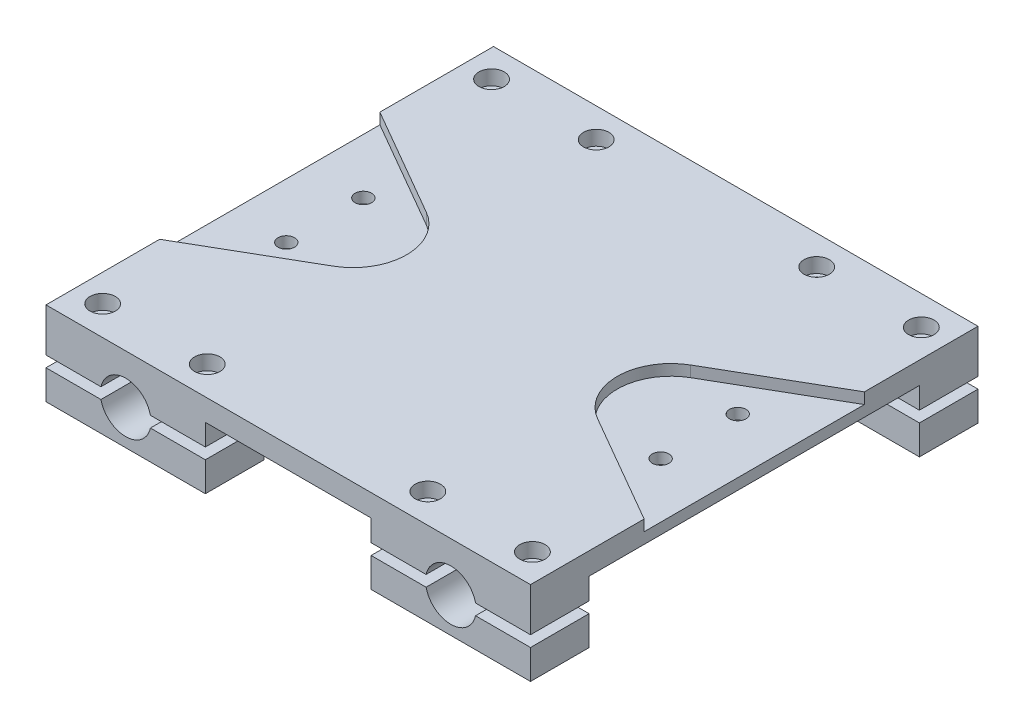
SolidWorks part; units mm, degrees
ref_plane "Front Plane" through (0, 0, 0) normal (0, 0, 1) x (1, 0, 0)
ref_plane "Top Plane" through (0, 0, 0) normal (0, 1, 0) x (1, 0, 0)
ref_plane "Right Plane" through (0, 0, 0) normal (1, 0, 0) x (0, 0, -1)
sketch "Sketch1" plane through (0, 0, 0) normal (0, 0, 1) x (1, 0, 0)
  line L0 (73.8188, 0) -> (0, 0) construction
  line L1 (-110, -15.875) -> (110, -15.875)
  line L2 (-110, -15.875) -> (-110, 15.875)
  line L3 (-110, 15.875) -> (110, 15.875)
  line L4 (110, -15.875) -> (110, 15.875)
  line L5 (-110, -15.875) -> (110, 15.875) construction
  line L6 (-110, 15.875) -> (110, -15.875) construction
  line L7 (0, 0) -> (-73.8187, 0) construction
  circle A1 centre (-73.8187, 0) radius 11.5
  circle A2 centre (73.8188, 0) radius 11.5
  point P0 (0, 0)
  dimension "D1" = 147.6375
  dimension "D4" = 23
  dimension "D2" = 31.75
  dimension "D3" = 220
extrude "Boss-Extrude1" add sketch "Sketch1" along normal blind 203.2
sketch "Sketch3" plane through (0, 0, 203.2) normal (0, 0, 1) x (1, 0, 0)
  line L0 (110, -15.875) -> (110, 15.875) construction
  line L1 (-110, 15.875) -> (110, 15.875)
  line L2 (-110, 15.875) -> (-110, 22.225)
  line L3 (-110, 22.225) -> (110, 22.225)
  line L4 (110, 15.875) -> (110, 22.225)
  dimension "D1" = 6.35
extrude "Boss-Extrude2" add sketch "Sketch3" against normal up to surface (203.2 mm away) up to face at (-62.3188, 0, 0)
sketch "Sketch4" plane through (-110, 0, 0) normal (-1, 0, 0) x (0, 0, 1)
  line L0 (203.2, -15.875) -> (0, -15.875) construction
  line L1 (26.6, -15.875) -> (176.6, -15.875)
  line L2 (26.6, -15.875) -> (26.6, 12.225)
  line L3 (26.6, 12.225) -> (176.6, 12.225)
  line L4 (176.6, -15.875) -> (176.6, 12.225)
  line L5 (0, 0) -> (26.6, 0) construction
  line L6 (26.6, 0) -> (176.6, 0) construction
  line L7 (176.6, 0) -> (203.2, 0) construction
  line L8 (203.2, 22.225) -> (203.2, -15.875) construction
  line L9 (0, 22.225) -> (203.2, 22.225) construction
  dimension "D1" = 10
  dimension "D2" = 150
extrude "Cut-Extrude1" cut sketch "Sketch4" against normal blind 253.2
sketch "Sketch5" plane through (0, 0, 0) normal (0, 0, -1) x (-1, 0, 0)
  line L0 (110, -15.875) -> (-110, -15.875) construction
  line L1 (-37.6375, -15.875) -> (37.6375, -15.875)
  line L2 (-37.6375, -15.875) -> (-37.6375, 12.225)
  line L3 (-37.6375, 12.225) -> (37.6375, 12.225)
  line L4 (37.6375, -15.875) -> (37.6375, 12.225)
  line L5 (-110, 22.225) -> (110, 22.225) construction
  line L6 (0, 0) -> (-37.6375, 0) construction
  line L7 (0, 0) -> (37.6375, 0) construction
  line L8 (-37.6375, 0) -> (-73.8188, 0) construction
  line L9 (-73.8188, 0) -> (-110, 0) construction
  line L10 (-110, -15.875) -> (-110, 22.225) construction
  dimension "D1" = 10
extrude "Cut-Extrude2" cut sketch "Sketch5" against normal blind 203.2
sketch "Sketch6" plane through (0, -15.875, 0) normal (0, -1, 0) x (1, 0, 0)
  line L0 (-110, 189.9) -> (-97.5688, 189.9) construction
  line L2 (-97.5688, 189.9) -> (-50.0688, 189.9) construction
  line L3 (-50.0688, 189.9) -> (-37.6375, 189.9) construction
  line L5 (-110, 13.3) -> (-97.5688, 13.3) construction
  line L6 (-110, 26.6) -> (-110, 0) construction
  line L7 (-97.5688, 13.3) -> (-50.0688, 13.3) construction
  line L8 (-50.0688, 13.3) -> (-37.6375, 13.3) construction
  line L9 (-37.6375, 26.6) -> (-37.6375, 0) construction
  line L10 (37.6375, 203.2) -> (37.6375, 176.6) construction
  line L11 (37.6375, 26.6) -> (37.6375, 0) construction
  line L12 (37.6375, 13.3) -> (50.0688, 13.3) construction
  line L13 (50.0688, 13.3) -> (97.5687, 13.3) construction
  line L14 (97.5687, 13.3) -> (110, 13.3) construction
  line L16 (-62.3188, 203.2) -> (-85.3187, 203.2) construction
  line L18 (110, 189.9) -> (97.5687, 189.9) construction
  line L19 (97.5687, 189.9) -> (50.0688, 189.9) construction
  line L20 (50.0688, 189.9) -> (37.6375, 189.9) construction
  line L22 (-62.3188, 203.2) -> (-85.3187, 203.2)
  line L23 (-85.3187, 203.2) -> (-85.3187, 0) construction
  line L24 (-110, 0) -> (-37.6375, 0) construction
  line L25 (-62.3188, 203.2) -> (-62.3188, 0) construction
  line L28 (-37.6375, 203.2) -> (-37.6375, 176.6) construction
  line L29 (-110, 203.2) -> (-110, 176.6) construction
  line L30 (110, 203.2) -> (110, 176.6) construction
  circle A0 centre (-50.0688, 189.9) radius 3.7258
  circle A1 centre (-97.5688, 189.9) radius 3.7258
  circle A2 centre (-97.5688, 13.3) radius 3.7258
  circle A3 centre (-50.0688, 13.3) radius 3.7258
  circle A4 centre (50.0688, 13.3) radius 3.7258
  circle A5 centre (97.5687, 13.3) radius 3.7258
  circle A6 centre (97.5687, 189.9) radius 3.7258
  circle A7 centre (50.0688, 189.9) radius 3.7258
  dimension "D1" = 7.4516
  dimension "D2" = 47.5
extrude "Cut-Extrude3" cut sketch "Sketch6" against normal blind 203.2 contours A4 | A5 | A3 | A2 | A1 | A0 | A7 | A6
sketch "Sketch7" plane through (0, 0, 0) normal (0, 0, -1) x (-1, 0, 0)
  line L0 (-110, -15.875) -> (-110, 22.225) construction
  line L1 (110, -2.5) -> (-110, -2.5)
  line L2 (110, -2.5) -> (110, 2.5)
  line L3 (110, 2.5) -> (-110, 2.5)
  line L4 (-110, -2.5) -> (-110, 2.5)
  line L5 (110, -2.5) -> (-110, 2.5) construction
  line L6 (110, 2.5) -> (-110, -2.5) construction
  point P0 (0, 0)
  dimension "D1" = 5
extrude "Cut-Extrude4" cut sketch "Sketch7" against normal blind 203.2
sketch "Sketch8" plane through (-110, 0, 0) normal (-1, 0, 0) x (0, 0, 1)
  line L0 (176.6, 12.225) -> (26.6, 12.225) construction
  line L1 (176.6, 12.225) -> (26.6, 12.225)
  line L2 (176.6, 12.225) -> (176.6, 22.225)
  line L3 (176.6, 22.225) -> (26.6, 22.225)
  line L4 (26.6, 12.225) -> (26.6, 22.225)
  line L5 (0, 22.225) -> (203.2, 22.225) construction
  line M4 (26.6, 12.225) -> (176.6, 12.225)
  line M8 (203.2, 22.225) -> (0, 22.225)
extrude "Boss-Extrude3" add sketch "Sketch8" along normal blind 132.4137 contours L4 L2 M4 M8
sketch "Sketch9" plane through (110, 0, 0) normal (1, 0, 0) x (0, 0, -1)
  line L0 (-176.6, 12.225) -> (-26.6, 12.225) construction
  line L1 (-176.6, 12.225) -> (-26.6, 12.225)
  line L2 (-176.6, 12.225) -> (-176.6, 22.225)
  line L3 (-176.6, 22.225) -> (-26.6, 22.225)
  line L4 (-26.6, 12.225) -> (-26.6, 22.225)
  line L5 (0, 22.225) -> (-203.2, 22.225) construction
extrude "Boss-Extrude4" add sketch "Sketch9" along normal blind 161.0473
ref_plane "Plane1" through (-110, 0, 0) normal (-1, 0, 0) x (0, 0, 1)
ref_plane "Plane2" through (110, 0, 0) normal (1, 0, 0) x (0, 0, -1)
split line "Split Line1"
split line "Split Line2"
sketch "Sketch10" plane through (0, 22.225, 0) normal (0, 1, 0) x (1, 0, 0)
  line L1 (0, 0) -> (0, -203.2) construction
  line L3 (110, 0) -> (-110, 0) construction
  line L4 (110, -203.2) -> (-110, -203.2) construction
  line L5 (-217.0137, -152.4) -> (245.6473, -152.4) construction
  circle A8 centre (-217.0137, -152.4) radius 3.7258
  circle A9 centre (-217.0137, -50.9667) radius 3.7258
  circle A10 centre (245.6473, -50.8) radius 3.7258
  circle A11 centre (245.6473, -152.4) radius 3.7258
  dimension "D1" = 7.4516
extrude "Cut-Extrude5" cut sketch "Sketch10" against normal blind 10
sketch "Sketch11" plane through (0, 22.225, 0) normal (0, 1, 0) x (1, 0, 0)
  circle A0 centre (97.5687, -13.3) radius 5.7625
  circle A1 centre (50.0688, -13.3) radius 5.7625
  circle A2 centre (97.5687, -189.9) radius 5.7625
  circle A3 centre (50.0688, -189.9) radius 5.7625
  circle A4 centre (-50.0688, -189.9) radius 5.7625
  circle A5 centre (-97.5688, -189.9) radius 5.7625
  circle A6 centre (-97.5688, -13.3) radius 5.7625
  circle A7 centre (-50.0688, -13.3) radius 5.7625
  dimension "D1" = 11.525
extrude "Cut-Extrude6" cut sketch "Sketch11" against normal blind 6.6675
sketch "Sketch12" plane through (0, 22.225, 0) normal (0, 1, 0) x (1, 0, 0)
  line L5 (-242.4137, -176.6) -> (-110, -176.6)
  line L6 (-242.4137, -176.6) -> (-242.4137, -26.6)
  line L7 (-242.4137, -26.6) -> (-110, -26.6)
  line L8 (-110, -176.6) -> (-110, -26.6)
  line L9 (271.0473, -176.6) -> (110, -176.6)
  line L10 (271.0473, -176.6) -> (271.0473, -26.6)
  line L11 (271.0473, -26.6) -> (110, -26.6)
  line L12 (110, -176.6) -> (110, -26.6)
extrude "Cut-Extrude8" cut sketch "Sketch12" against normal blind 82
sketch "Sketch13" plane through (0, 22.225, 0) normal (0, 1, 0) x (1, 0, 0)
  line L0 (110, -51.6) -> (60, -80.4675)
  line L1 (110, -12.2237) -> (110, 12.2238) construction
  line L3 (60, -122.7325) -> (110, -151.6)
  line L4 (110, -151.6) -> (110, -51.6)
  line L5 (110, -51.6) -> (110, 0) construction
  line L9 (110, -203.2) -> (110, -151.6) construction
  line L10 (60, -122.7325) -> (60, -80.4675) construction
  line L11 (0, 0) -> (0, -203.2) construction
  line L12 (-60, -122.7325) -> (-60, -80.4675) construction
  line L13 (-110, -151.6) -> (-110, -51.6)
  line L14 (-60, -122.7325) -> (-110, -151.6)
  line L15 (-110, -51.6) -> (-60, -80.4675)
  line L17 (85, -66.0338) -> (85, -84.1) construction
  line L18 (85, -119.1) -> (85, -84.1) construction
  line L19 (85, -119.1) -> (85, -137.1662) construction
  arc A0 (60, -122.7325) -> (60, -80.4675) centre (72.2008, -101.6) cw
  arc A1 (-60, -122.7325) -> (-60, -80.4675) centre (-72.2008, -101.6) ccw
  circle A2 centre (85, -84.1) radius 3.75
  circle A3 centre (85, -119.1) radius 3.75
  point P8 (0, 0)
  point P9 (110, 0)
  point P11 (114.478, -212.2087)
  point P15 (0, 0)
  point P16 (0, 0)
  point P17 (0, 0)
  point P31 (0, 0)
  point P32 (0, 0)
  dimension "D4" = 24.4017
  dimension "D5" = 24.4017
  dimension "D6" = 7.5
  dimension "D1" = 60
  dimension "D2" = 60
  dimension "D3" = 100
  dimension "D7" = 35
extrude "Cut-Extrude10" cut sketch "Sketch13" against normal blind 5 contours A0 L3 L4 L0 A3 A2 | L14 A1 L15 L13 | A3 | A2
sketch "Sketch16" plane through (0, 17.225, 0) normal (0, 1, 0) x (1, 0, 0)
  line L0 (0, -203.2) -> (0, 0) construction
  line L1 (110, -203.2) -> (-110, -203.2) construction
  circle A0 centre (-85, -84.1) radius 3.75
  circle A3 centre (85, -119.1) radius 3.75
  circle A4 centre (85, -119.1) radius 3.75
  circle A5 centre (85, -84.1) radius 3.75
  circle A6 centre (85, -84.1) radius 3.75
  circle A9 centre (-85, -119.1) radius 3.75
  dimension "D2" = 0
  dimension "D3" = 0
extrude "Cut-Extrude11" cut sketch "Sketch16" against normal blind 5
